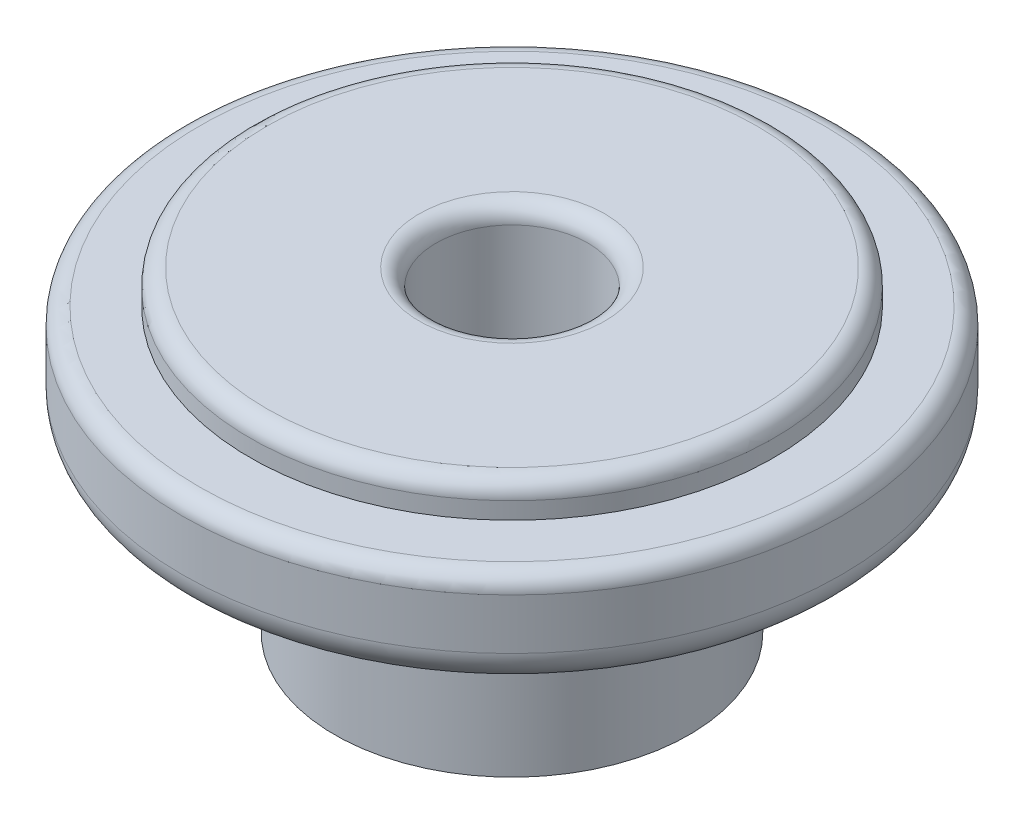
SolidWorks part; units mm, degrees
ref_plane "Front Plane" through (0, 0, 0) normal (0, 0, 1) x (1, 0, 0)
ref_plane "Top Plane" through (0, 0, 0) normal (0, 1, 0) x (1, 0, 0)
ref_plane "Right Plane" through (0, 0, 0) normal (1, 0, 0) x (0, 0, -1)
sketch "Sketch1" plane through (0, 0, 0) normal (0, 0, 1) x (1, 0, 0)
  line L0 (0, 0) -> (-2.2479, 0) construction
  line L1 (-2.2479, 0) -> (-2.2479, 9.35)
  line L2 (-2.2479, 9.35) -> (-7.7479, 9.35)
  line L3 (-7.7479, 9.35) -> (-7.7479, 8.35)
  line L4 (-7.7479, 8.35) -> (-9.7479, 8.35)
  line L5 (-9.7479, 8.35) -> (-9.7479, 6.35)
  line L6 (-2.2479, 0) -> (-5.2479, 0)
  line L7 (-5.2479, 0) -> (-5.2479, 6.35)
  line L8 (-5.2479, 6.35) -> (-7.7479, 6.35)
  line L9 (-7.7479, 6.35) -> (-9.7479, 6.35) construction
  line L10 (0, 0) -> (0, 1.4085) construction
  arc A0 (-9.7479, 6.35) -> (-7.7479, 6.35) centre (-8.7479, 6.35) ccw
  arc A1 (-7.7479, 6.35) -> (-9.7479, 6.35) centre (-8.7479, 6.35) ccw construction
  dimension "D1" = 2.2479
  dimension "D2" = 6.35
  dimension "D3" = 3
  dimension "D4" = 5.5
  dimension "D5" = 2
  dimension "D6" = 1
  dimension "D7" = 2
revolve "Revolve1" add sketch "Sketch1" angle 360 about L10
fillet "Fillet1" radius 0.5 3 edges at (0, 8.35, -9.7479) (0, 9.35, -7.7479) (0, 9.35, -2.2479)
